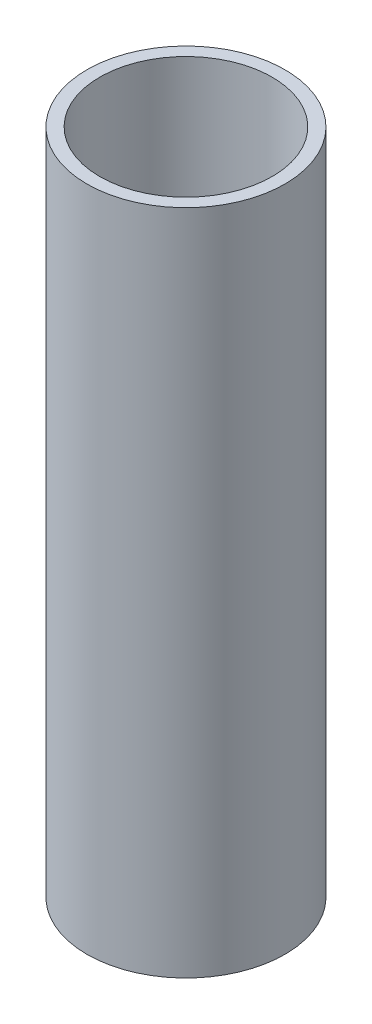
SolidWorks part; units mm, degrees
material "PE High Density"
ref_plane "Front Plane" through (0, 0, 0) normal (0, 0, 1) x (1, 0, 0)
ref_plane "Top Plane" through (0, 0, 0) normal (0, 1, 0) x (1, 0, 0)
ref_plane "Right Plane" through (0, 0, 0) normal (1, 0, 0) x (0, 0, -1)
sketch "Sketch1" plane through (0, 0, 0) normal (0, 1, 0) x (1, 0, 0)
  circle A0 centre (0, 0) radius 26.2509
  circle A1 centre (0, 0) radius 30.1625
  dimension "D1" = 60.325
  dimension "D2" = 52.5018
extrude "Boss-Extrude1" add sketch "Sketch1" along normal blind 203.2
